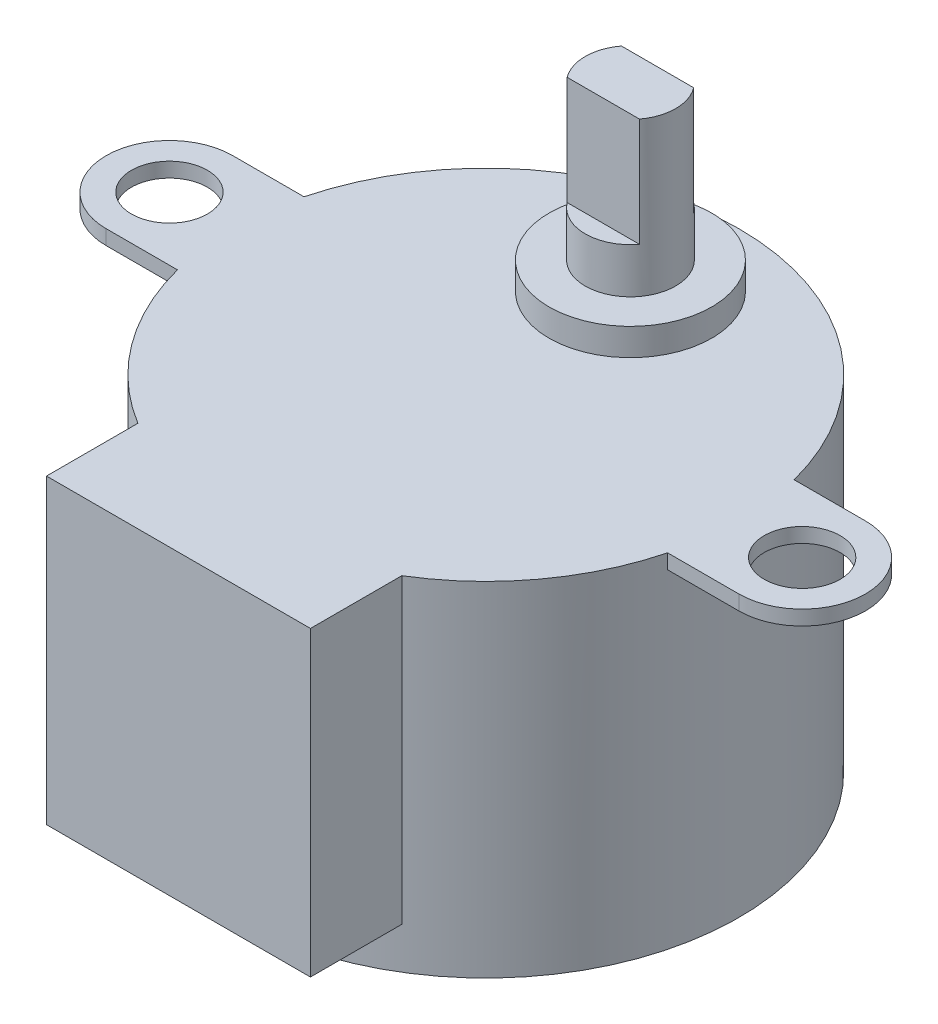
SolidWorks part; units mm, degrees
ref_plane "Front Plane" through (0, 0, 0) normal (0, 0, 1) x (1, 0, 0)
ref_plane "Top Plane" through (0, 0, 0) normal (0, 1, 0) x (1, 0, 0)
ref_plane "Right Plane" through (0, 0, 0) normal (1, 0, 0) x (0, 0, -1)
sketch "Sketch1" plane through (0, 0, 0) normal (0, 1, 0) x (1, 0, 0)
  circle A0 centre (0, 0) radius 14
  dimension "D1" = 28
extrude "Boss-Extrude1" add sketch "Sketch1" against normal blind 19
sketch "Sketch2" plane through (0, 0, 0) normal (0, 1, 0) x (1, 0, 0)
  line L0 (-17.5, 0) -> (17.5, 0) construction
  line L1 (-17.5, 3.5) -> (17.5, 3.5)
  line L2 (-17.5, -3.5) -> (17.5, -3.5)
  arc A0 (-17.5, 3.5) -> (-17.5, -3.5) centre (-17.5, 0) ccw
  arc A1 (17.5, -3.5) -> (17.5, 3.5) centre (17.5, 0) ccw
  point P2 (0, 0)
  dimension "D2" = 35
  dimension "D1" = 7
extrude "Boss-Extrude2" add sketch "Sketch2" against normal blind 0.8128
sketch "Sketch3" plane through (0, 0, 0) normal (0, 1, 0) x (1, 0, 0)
  circle A0 centre (-17.5, 0) radius 2.1
  circle A1 centre (17.5, 0) radius 2.1
  dimension "D1" = 4.2
extrude "Cut-Extrude1" cut sketch "Sketch3" against normal blind 0.8128
sketch "Sketch4" plane through (0, 0, 0) normal (0, 1, 0) x (1, 0, 0)
  circle A0 centre (0, 8) radius 4.5
  dimension "D1" = 9
  dimension "D2" = 8
extrude "Boss-Extrude3" add sketch "Sketch4" along normal blind 1.5
sketch "Sketch5" plane through (0, 1.5, 0) normal (0, 1, 0) x (1, 0, 0)
  circle A0 centre (0, 8) radius 2.5
  dimension "D1" = 5
extrude "Boss-Extrude4" add sketch "Sketch5" along normal blind 10 from offset 1.5 offset against normal yes
sketch "Sketch6" plane through (0, 10, 0) normal (0, 1, 0) x (1, 0, 0)
  line L0 (-2, 9.5) -> (2, 9.5)
  line L1 (-2, 6.5) -> (2, 6.5)
  circle A1 centre (0, 8) radius 2.5
  circle A2 centre (0, 8) radius 2.5
  circle M4 centre (0, 8) radius 2.5
  dimension "D2" = 3
  dimension "D3" = 1.5
  dimension "D1" = 0
extrude "Cut-Extrude2" cut sketch "Sketch6" against normal blind 6 contours L0 M4 | L1 M4
sketch "Sketch7" plane through (0, 0, 0) normal (0, 1, 0) x (1, 0, 0)
  line L1 (-7.3, -11.9461) -> (7.3, -11.9461)
  line L2 (-7.3, -11.9461) -> (-7.3, -17)
  line L3 (-7.3, -17) -> (7.3, -17)
  line L4 (7.3, -11.9461) -> (7.3, -17)
  line L5 (0, -17) -> (0, -11.9461) construction
  line L6 (-7.3, -14.4731) -> (7.3, -14.4731) construction
  arc A0 (-13.5554, -3.5) -> (13.5554, -3.5) centre (0, 0) ccw construction
  point P140 (0, -14.4731)
  dimension "D1" = 14.6
  dimension "D2" = 17
extrude "Boss-Extrude5" add sketch "Sketch7" against normal blind 16.7
